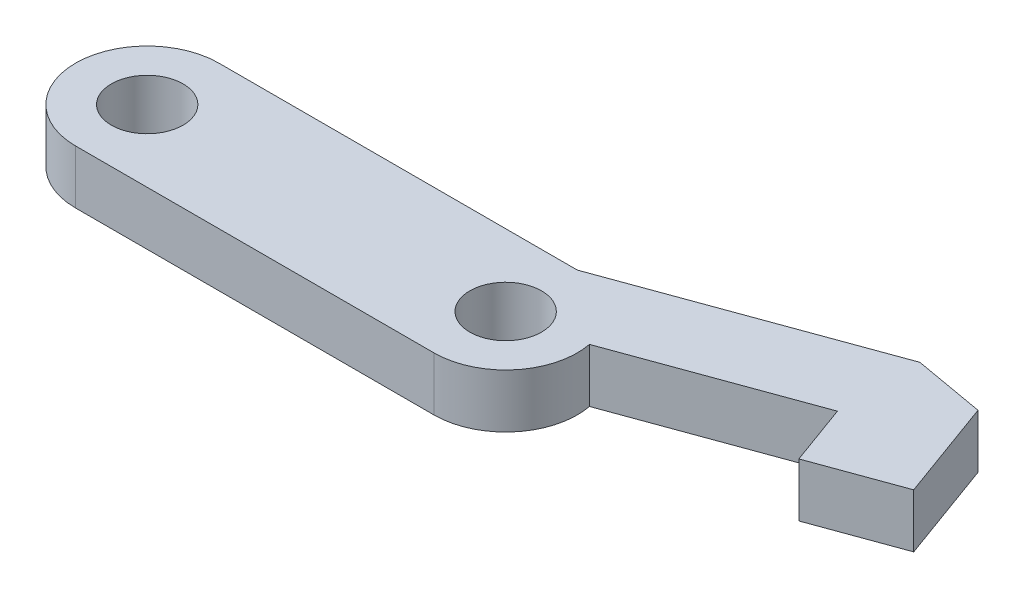
SolidWorks part; units mm, degrees
material "Oak"
ref_plane "Front" through (0, 0, 0) normal (0, 0, 1) x (1, 0, 0)
ref_plane "Top" through (0, 0, 0) normal (0, 1, 0) x (1, 0, 0)
ref_plane "Right" through (0, 0, 0) normal (1, 0, 0) x (0, 0, -1)
sketch "Sketch1" plane through (0, 0, 0) normal (0, 1, 0) x (1, 0, 0)
  line L0 (0, 86.6597) -> (0, -74.0832) construction
  line L1 (0, 0) -> (-100, 0) construction
  line L2 (0, -20) -> (-100, -20)
  line L3 (0, 20) -> (-100, 20)
  line L4 (0, 20) -> (70.0432, 45.4937)
  line L5 (70.0432, 45.4937) -> (89.7394, 42.0207)
  line L6 (89.7394, 42.0207) -> (100, 13.8299)
  line L7 (100, 13.8299) -> (76.5077, 5.2794)
  line L8 (76.5077, 5.2794) -> (70.3513, 22.1939)
  line L9 (70.3513, 22.1939) -> (19.6474, 3.7391)
  arc A0 (0, -20) -> (0, 20) centre (0, 0) ccw
  arc A1 (-100, 20) -> (-100, -20) centre (-100, 0) ccw
  point P5 (-50, 0)
  dimension "D2" = 20
  dimension "D1" = 100
  dimension "D3" = 70
  dimension "D4" = 22
  dimension "D5" = 100
  dimension "D6" = 60
  dimension "D7" = 90
  dimension "D8" = 18
  dimension "D9" = 20
  dimension "D10" = 70
  dimension "D11" = 25
  dimension "D12" = 180
extrude "Boss-Extrude1" add sketch "Sketch1" along normal blind 15 contours L3 A1 L2 A0 | A0 L9 L8 L7 L6 L5 L4
hole_wizard "Ø20.0mm 맞춤핀 구멍1" positions "Sketch3" profile "Sketch2" hole size "Ø20.0" standard "Ansi Metric" end condition through all
sketch "Sketch3" plane through (0, 15, 0) normal (0, 1, 0) x (1, 0, 0)
  arc A0 (-100, 20) -> (-100, -20) centre (-100, 0) ccw construction
  point P0 (-100, 0)
  point P2 (0, 0)
  dimension "D1" = 0
sketch "Sketch2" plane through (-100, 15, 0) normal (1, 0, 0) x (0, 0, 1)
  line L0 (0, 0) -> (0, 15)
  line L1 (0, 15) -> (10, 15)
  line L2 (10, 15) -> (10, 0)
  line L5 (10, 0) -> (0, 0)
  line L11 (0, -6.35) -> (0, 107.95) construction
  dimension "Thru Hole Dia." = 20
  dimension "Thru Hole Depth" = 15
scale "축척1" scale about centroid uniform scaling yes scale factor 0.3
